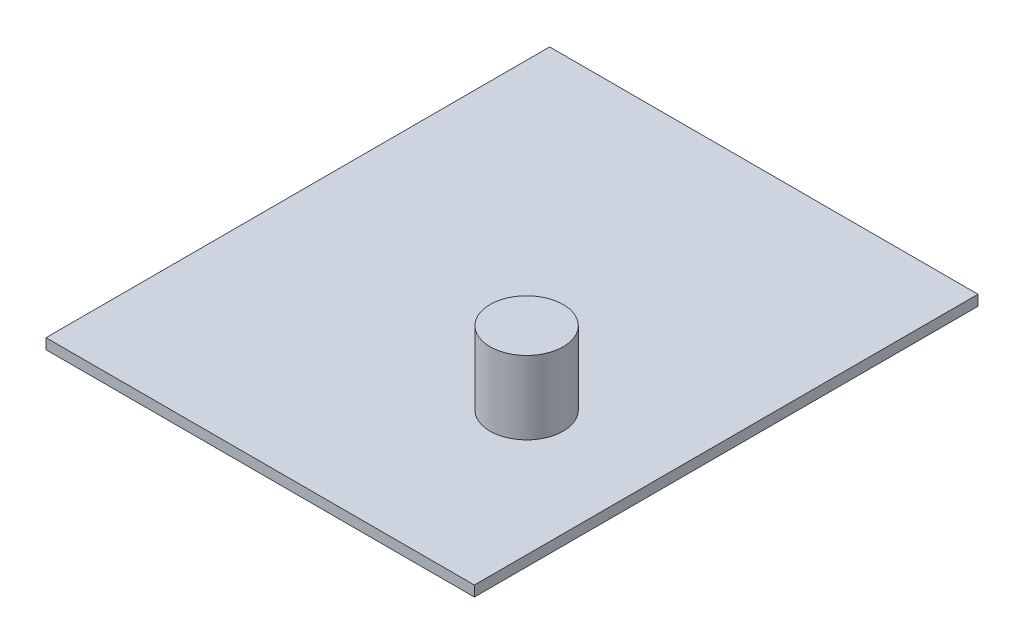
SolidWorks part; units mm, degrees
ref_plane "Front Plane" through (0, 0, 0) normal (0, 0, 1) x (1, 0, 0)
ref_plane "Top Plane" through (0, 0, 0) normal (0, 1, 0) x (1, 0, 0)
ref_plane "Right Plane" through (0, 0, 0) normal (1, 0, 0) x (0, 0, -1)
sketch "Sketch1" plane through (0, 0, 0) normal (0, 1, 0) x (1, 0, 0)
  line L1 (-17.6673, 15.9155) -> (23.3327, 15.9155)
  line L2 (-17.6673, 15.9155) -> (-17.6673, -32.2845)
  line L3 (-17.6673, -32.2845) -> (23.3327, -32.2845)
  line L4 (23.3327, 15.9155) -> (23.3327, -32.2845)
  dimension "D1" = 41
  dimension "D2" = 48.2
extrude "Boss-Extrude1" add sketch "Sketch1" along normal blind 1
sketch "Sketch8" plane through (0, 1, 0) normal (0, 1, 0) x (1, 0, 0)
  line L0 (-17.6673, -32.2845) -> (23.3327, -32.2845) construction
  line L1 (23.3327, -32.2845) -> (23.3327, 15.9155) construction
  circle A0 centre (11.3327, -15.2845) radius 3.5
  dimension "D1" = 7
  dimension "D2" = 17
  dimension "D3" = 12
extrude "Boss-Extrude2" add sketch "Sketch8" along normal blind 7
